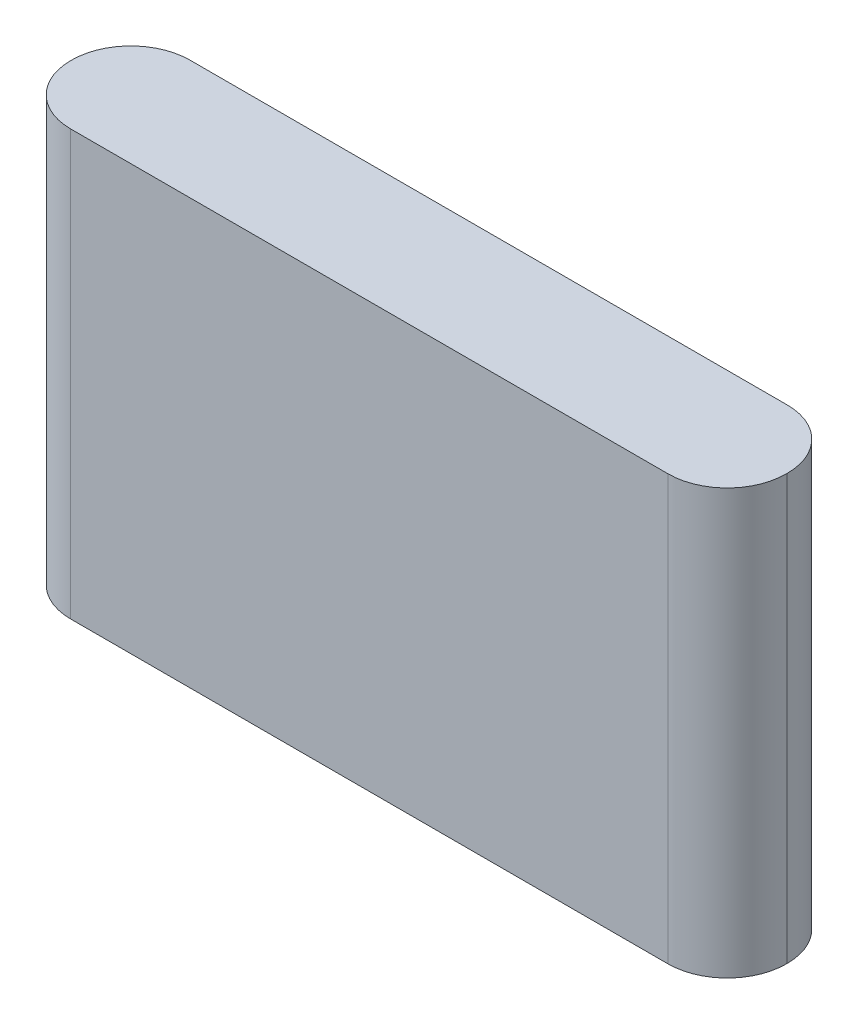
SolidWorks part; units mm, degrees
material "Custom Plastic"
ref_plane "Front Plane" through (0, 0, 0) normal (0, 0, 1) x (1, 0, 0)
ref_plane "Top Plane" through (0, 0, 0) normal (0, 1, 0) x (1, 0, 0)
ref_plane "Right Plane" through (0, 0, 0) normal (1, 0, 0) x (0, 0, -1)
sketch "Sketch1" plane through (0, 0, 0) normal (0, 1, 0) x (1, 0, 0)
  line L1 (-43, 7.165) -> (43, 7.165)
  line L2 (-43, 7.165) -> (-43, -7.165)
  line L3 (-43, -7.165) -> (43, -7.165)
  line L4 (43, 7.165) -> (43, -7.165)
  line L5 (-43, 7.165) -> (43, -7.165) construction
  line L6 (-43, -7.165) -> (43, 7.165) construction
  point P0 (0, 0)
  dimension "D1" = 14.33
  dimension "D2" = 86
extrude "Boss-Extrude1" add sketch "Sketch1" along normal blind 51
fillet "Fillet1" radius 7.1 4 edges at (43, 25.5, -7.165) (43, 25.5, 7.165) (-43, 25.5, -7.165) (-43, 25.5, 7.165)
